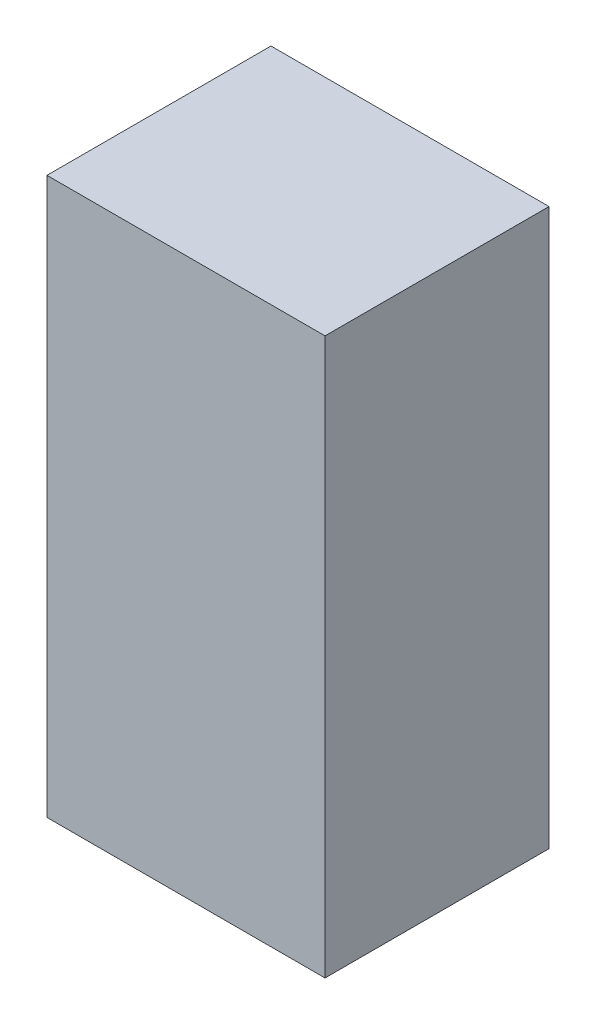
SolidWorks part; units mm, degrees
ref_plane "Front Plane" through (0, 0, 0) normal (0, 0, 1) x (1, 0, 0)
ref_plane "Top Plane" through (0, 0, 0) normal (0, 1, 0) x (1, 0, 0)
ref_plane "Right Plane" through (0, 0, 0) normal (1, 0, 0) x (0, 0, -1)
sketch "Sketch1" plane through (0, 0, 0) normal (0, 1, 0) x (1, 0, 0)
  line L1 (-18, 14.5) -> (18, 14.5)
  line L2 (-18, 14.5) -> (-18, -14.5)
  line L3 (-18, -14.5) -> (18, -14.5)
  line L4 (18, 14.5) -> (18, -14.5)
  line L5 (-18, 14.5) -> (18, -14.5) construction
  line L6 (-18, -14.5) -> (18, 14.5) construction
  point P0 (0, 0)
  dimension "D1" = 36
  dimension "D2" = 29
extrude "Boss-Extrude1" add sketch "Sketch1" along normal blind 72
